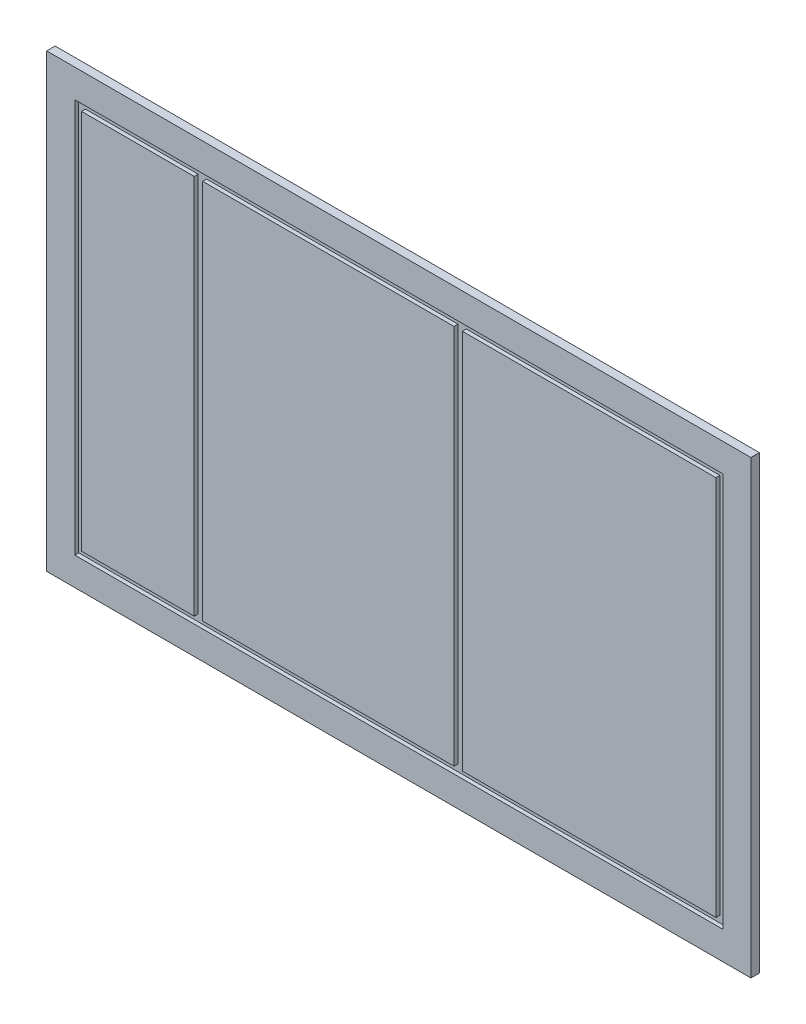
SolidWorks part; units mm, degrees
material "Erable"
ref_plane "Plan de face" through (0, 0, 0) normal (0, 0, 1) x (1, 0, 0)
ref_plane "Plan de dessus" through (0, 0, 0) normal (0, 1, 0) x (1, 0, 0)
ref_plane "Plan de droite" through (0, 0, 0) normal (1, 0, 0) x (0, 0, -1)
sketch "Esquisse1" plane through (0, 0, 0) normal (0, 0, 1) x (1, 0, 0)
  line L1 (625, -400) -> (-625, -400)
  line L2 (625, -400) -> (625, 400)
  line L3 (625, 400) -> (-625, 400)
  line L4 (-625, -400) -> (-625, 400)
  line L5 (625, -400) -> (-625, 400) construction
  line L6 (625, 400) -> (-625, -400) construction
  point P0 (0, 0)
  dimension "D1" = 800
  dimension "D2" = 1250
extrude "Boss.-Extru.1" add sketch "Esquisse1" along normal blind 15
sketch "Esquisse2" plane through (0, 0, 15) normal (0, 0, 1) x (1, 0, 0)
  line L0 (625, 400) -> (-625, 400) construction
  line L1 (-625, 400) -> (-625, -400) construction
  line L3 (563, -338) -> (-563, -338)
  line L4 (563, -338) -> (563, 338)
  line L5 (563, 338) -> (-563, 338)
  line L6 (-563, -338) -> (-563, 338)
  line L7 (575, -350) -> (-575, -350)
  line L8 (575, -350) -> (575, 350)
  line L9 (575, 350) -> (-575, 350)
  line L10 (-575, -350) -> (-575, 350)
  line L11 (563, -338) -> (-563, 338) construction
  line L12 (563, 338) -> (-563, -338) construction
  point P0 (0, 0)
  point P6 (0, 0)
  point P11 (0, 0)
  dimension "D1" = 700
  dimension "D2" = 1150
  dimension "D3" = 50
  dimension "D4" = 50
  dimension "D5" = 12
  dimension "D6" = 12
extrude "Enlèv. mat.-Extru.1" cut sketch "Esquisse2" against normal blind 7
sketch "Esquisse4" plane through (0, 0, 15) normal (0, 0, 1) x (1, 0, 0)
  line L0 (563, 338) -> (-563, 338) construction
  line L1 (-363, 338) -> (-348, 338)
  line L2 (-363, 338) -> (-363, -338)
  line L3 (-363, -338) -> (-348, -338)
  line L4 (-348, 338) -> (-348, -338)
  line L5 (-563, -338) -> (563, -338) construction
  line L6 (563, 338) -> (-563, 338) construction
  line L7 (98, 338) -> (113, 338)
  line L8 (98, 338) -> (98, -338)
  line L9 (98, -338) -> (113, -338)
  line L10 (113, 338) -> (113, -338)
  line L11 (563, -338) -> (563, 338) construction
  line L12 (-563, 338) -> (-563, -338) construction
  dimension "D1" = 15
  dimension "D2" = 15
  dimension "D3" = 450
  dimension "D4" = 200
extrude "Enlèv. mat.-Extru.2" cut sketch "Esquisse4" against normal blind 7
